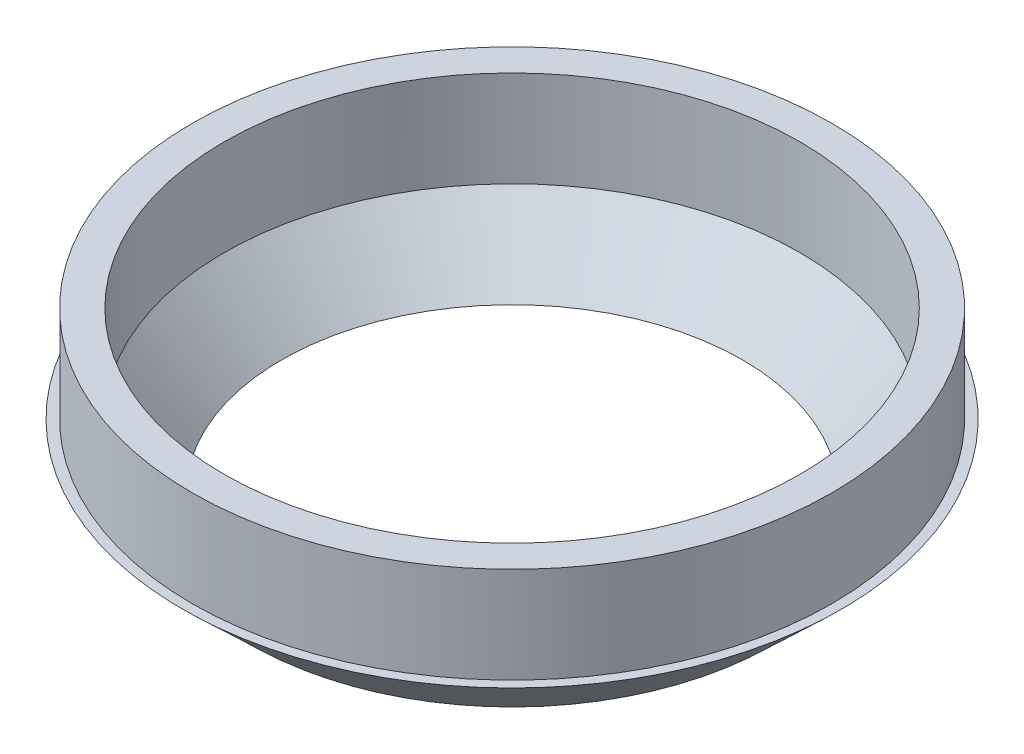
SolidWorks part; units mm, degrees
ref_plane "Front Plane" through (0, 0, 0) normal (0, 0, 1) x (1, 0, 0)
ref_plane "Top Plane" through (0, 0, 0) normal (0, 1, 0) x (1, 0, 0)
ref_plane "Right Plane" through (0, 0, 0) normal (1, 0, 0) x (0, 0, -1)
sketch "Sketch2" plane through (0, 0, 0) normal (0, 0, 1) x (1, 0, 0)
  line L0 (0, 0) -> (0, 12.7) construction
  line L1 (-45.72, 0) -> (-52.07, 0)
  line L2 (-57.15, 12.7) -> (-65.405, 12.7)
  line L3 (-65.405, 12.7) -> (-52.07, 0)
  line L4 (-57.15, 12.7) -> (-45.72, 0)
  dimension "D1" = 65.405
  dimension "D2" = 57.15
  dimension "D3" = 45.72
  dimension "D4" = 52.07
  dimension "D5" = 12.7
revolve "Revolve1" add sketch "Sketch2" angle 360 about L0
sketch "Sketch3" plane through (0, 12.7, 0) normal (0, 1, 0) x (1, 0, 0)
  circle A0 centre (0, 0) radius 57.15
  circle A1 centre (0, 0) radius 63.5
  dimension "D1" = 114.3
  dimension "D2" = 127
extrude "Boss-Extrude1" add sketch "Sketch3" along normal blind 19.05
equation "\"Inside Diamter\"= 5in"
equation "\"Inside Thickness\"= 0.5in"
equation "\"D2@Sketch2\"=(\"Inside Diamter\" - \"Inside Thickness\")/2"
equation "\"Bottom Diameter\"= 3.6"
equation "\"D3@Sketch2\" = \"Bottom Diameter\" / 2"
equation "\"D4@Sketch2\"= ( \"Bottom Diameter\" + \"Inside Thickness\" ) / 2"
equation "\"D1@Sketch3\"=\"Inside Diamter\"-\"Inside Thickness\""
equation "\"D2@Sketch3\"=\"Inside Diamter\""
